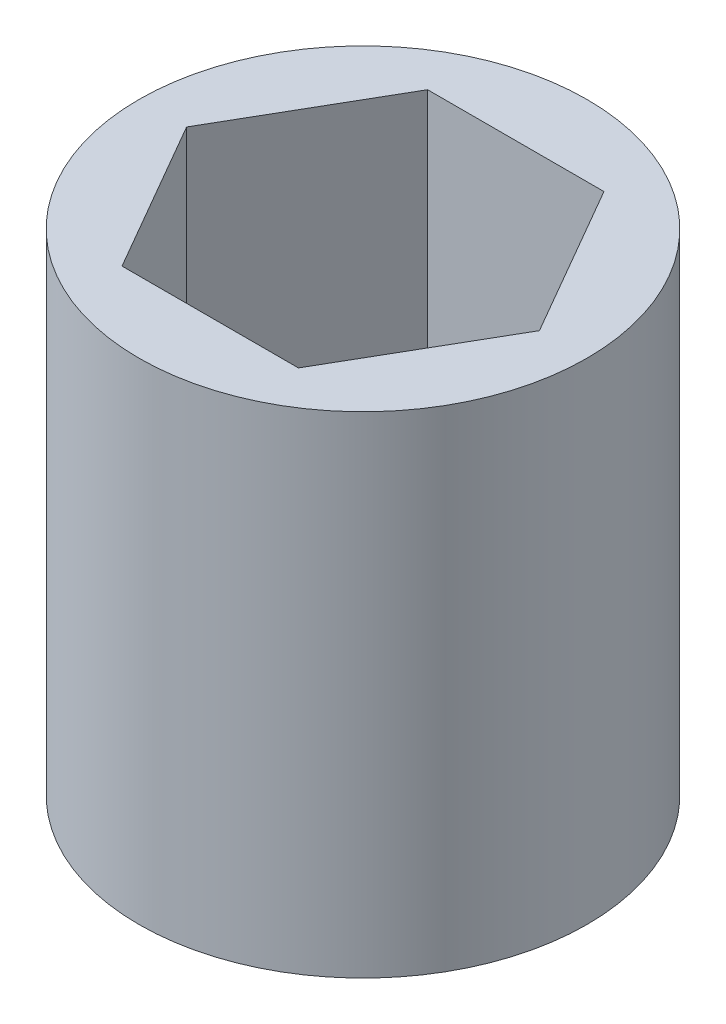
SolidWorks part; units mm, degrees
material "Markforged"
ref_plane "Front Plane" through (0, 0, 0) normal (0, 0, 1) x (1, 0, 0)
ref_plane "Top Plane" through (0, 0, 0) normal (0, 1, 0) x (1, 0, 0)
ref_plane "Right Plane" through (0, 0, 0) normal (1, 0, 0) x (0, 0, -1)
sketch "Sketch1" plane through (0, 0, 0) normal (0, 1, 0) x (1, 0, 0)
  line L1 (1.3748, -2.3813) -> (2.7496, 0)
  line L2 (2.7496, 0) -> (1.3748, 2.3812)
  line L3 (1.3748, 2.3812) -> (-1.3748, 2.3812)
  line L4 (-1.3748, 2.3812) -> (-2.7496, 0)
  line L5 (-2.7496, 0) -> (-1.3748, -2.3813)
  line L6 (-1.3748, -2.3813) -> (1.3748, -2.3813)
  circle A0 centre (0, 0) radius 3.4925
  circle A1 centre (0, 0) radius 2.3813 construction
  dimension "D1" = 6.985
  dimension "D2" = 4.7625
extrude "Boss-Extrude1" add sketch "Sketch1" along normal mid plane 7.6454
